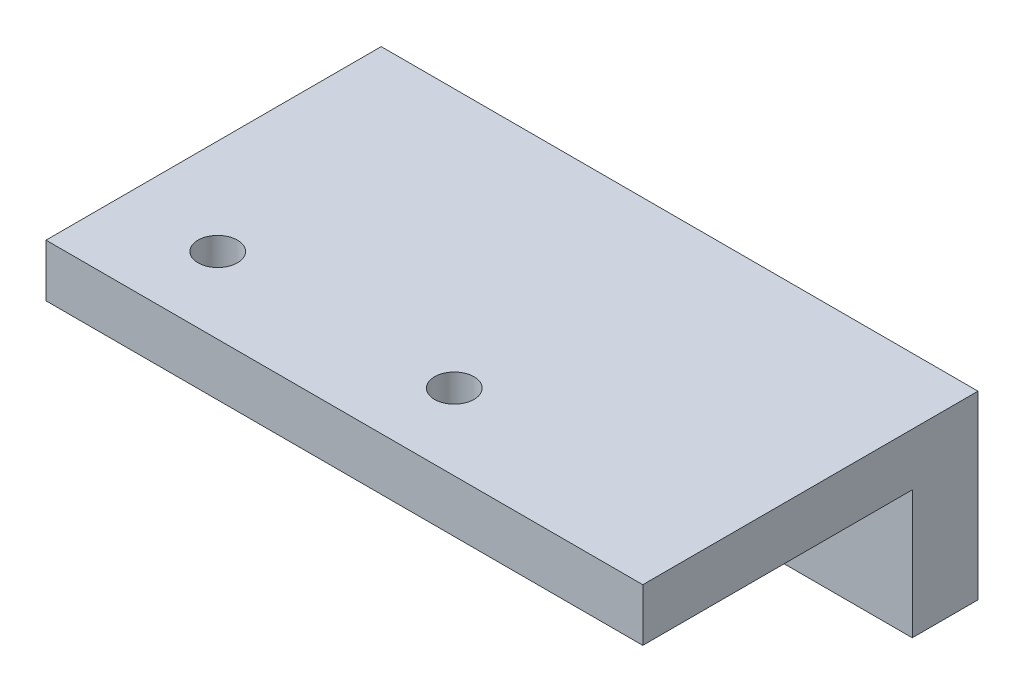
SolidWorks part; units mm, degrees
ref_plane "Front Plane" through (0, 0, 0) normal (0, 0, 1) x (1, 0, 0)
ref_plane "Top Plane" through (0, 0, 0) normal (0, 1, 0) x (1, 0, 0)
ref_plane "Right Plane" through (0, 0, 0) normal (1, 0, 0) x (0, 0, -1)
sketch "Sketch1" plane through (0, 0, 0) normal (0, 1, 0) x (1, 0, 0)
  line L1 (0, 0) -> (45.4, 0)
  line L2 (0, 0) -> (0, 25.5)
  line L3 (0, 25.5) -> (45.4, 25.5)
  line L4 (45.4, 0) -> (45.4, 25.5)
  line L5 (0, 0) -> (45.4, 25.5) construction
  line L6 (0, 25.5) -> (45.4, 0) construction
  point P4 (22.7, 12.75)
  dimension "D1" = 25.5
  dimension "D2" = 45.4
extrude "Boss-Extrude1" add sketch "Sketch1" along normal blind 4
sketch "Sketch2" plane through (0, 0, 0) normal (0, -1, 0) x (1, 0, 0)
  line L0 (0, -25.5) -> (0, 0) construction
  line L1 (45.4, -25.5) -> (0, -25.5)
  line L2 (45.4, -25.5) -> (45.4, -20.5)
  line L3 (45.4, -20.5) -> (0, -20.5)
  line L4 (0, -25.5) -> (0, -20.5)
  line L5 (45.4, -25.5) -> (0, -20.5) construction
  line L6 (45.4, -20.5) -> (0, -25.5) construction
  point P5 (22.7, -23)
  dimension "D1" = 5
extrude "Boss-Extrude2" add sketch "Sketch2" along normal blind 9.75
sketch "Sketch3" plane through (0, 4, 0) normal (0, 1, 0) x (1, 0, 0)
  circle A0 centre (7.2789, 5.7844) radius 1.5
  circle A1 centre (25.277, 5.7827) radius 1.5
  dimension "D1" = 3
  dimension "D2" = 3
extrude "Cut-Extrude1" cut sketch "Sketch3" against normal blind 10
sketch "Sketch7" plane through (0, 0, -20.5) normal (0, 0, 1) x (1, 0, 0)
  circle A0 centre (32.4, -4.8816) radius 1.65
  circle A1 centre (13, -4.8816) radius 1.65
  dimension "D1" = 3.3
extrude "Cut-Extrude3" cut sketch "Sketch7" against normal blind 10
